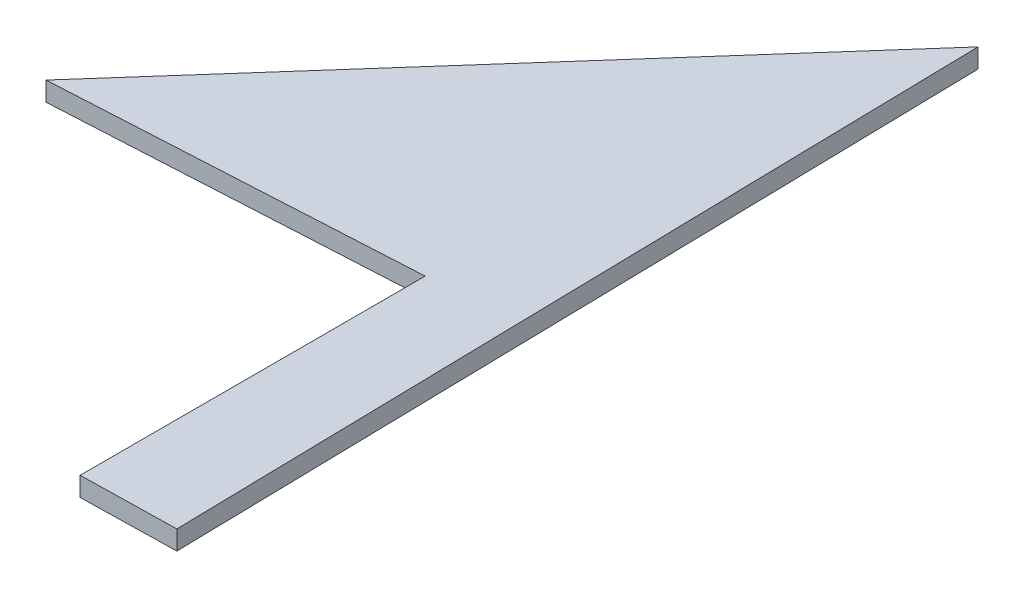
SolidWorks part; units mm, degrees
ref_plane "Plan de face" through (0, 0, 0) normal (0, 0, 1) x (1, 0, 0)
ref_plane "Plan de dessus" through (0, 0, 0) normal (0, 1, 0) x (1, 0, 0)
ref_plane "Plan de droite" through (0, 0, 0) normal (1, 0, 0) x (0, 0, -1)
sketch "Esquisse1" plane through (0, 0, 0) normal (0, 1, 0) x (1, 0, 0)
  line L0 (37.3826, 2.0572) -> (37.3826, -33.8343)
  line L1 (37.3826, -33.8343) -> (47.2457, -33.631)
  line L2 (47.2457, -33.631) -> (45.4917, 51.4669)
  line L3 (45.4917, 51.4669) -> (0, 0)
  line L4 (0, 0) -> (37.3826, 2.0572)
  point P5 (0, 0)
extrude "Boss.-Extru.1" add sketch "Esquisse1" along normal blind 2
